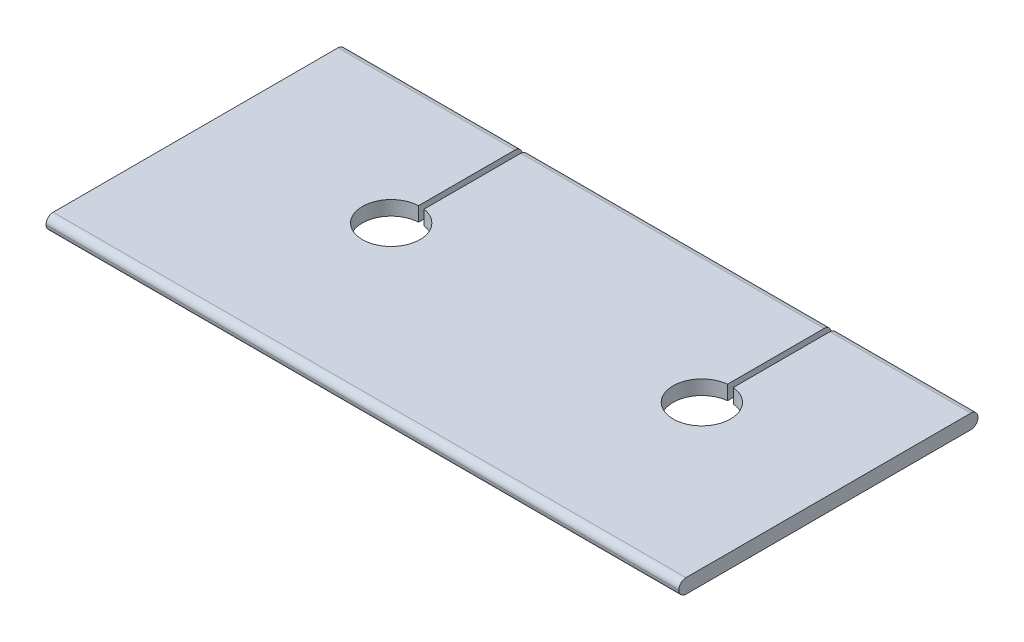
SolidWorks part; units mm, degrees
ref_plane "Front Plane" through (0, 0, 0) normal (0, 0, 1) x (1, 0, 0)
ref_plane "Top Plane" through (0, 0, 0) normal (0, 1, 0) x (1, 0, 0)
ref_plane "Right Plane" through (0, 0, 0) normal (1, 0, 0) x (0, 0, -1)
sketch "Sketch1" plane through (0, 0, 0) normal (1, 0, 0) x (0, 0, -1)
  line L1 (12.38, 0.625) -> (-12.38, 0.625)
  line L2 (13, 0.005) -> (13, -0.005)
  line L3 (12.38, -0.625) -> (-12.38, -0.625)
  line L4 (-13, 0.005) -> (-13, -0.005)
  line L5 (13, 0.625) -> (-13, -0.625) construction
  line L6 (13, -0.625) -> (-13, 0.625) construction
  arc A0 (13, -0.005) -> (12.38, -0.625) centre (12.38, -0.005) cw
  arc A1 (12.38, 0.625) -> (13, 0.005) centre (12.38, 0.005) cw
  arc A2 (-12.38, -0.625) -> (-13, -0.005) centre (-12.38, -0.005) cw
  arc A3 (-12.38, 0.625) -> (-13, 0.005) centre (-12.38, 0.005) ccw
  point P0 (0, 0)
  dimension "D3" = 0.62
  dimension "D1" = 26
  dimension "D2" = 1.25
extrude "Boss-Extrude1" add sketch "Sketch1" along normal blind 55
sketch "Sketch2" plane through (0, 0.625, 0) normal (0, 1, 0) x (1, 0, 0)
  line L0 (55, 13) -> (0, 13) construction
  line L2 (55, 12.38) -> (55, -12.38) construction
  line L3 (15.75, -13.4248) -> (15.25, -13.4248)
  line L4 (15.8823, 3.9706) -> (15.8823, 17.1341)
  line L5 (15.8823, 17.1341) -> (15.3823, 17.1341)
  line L6 (15.3823, 3.9972) -> (15.3823, 17.1341)
  line L9 (35.75, -13.4248) -> (35.25, -13.4248)
  line L10 (42.7463, 3.9878) -> (42.7463, 16.4248)
  line L11 (42.7463, 16.4248) -> (42.2463, 16.4248)
  line L12 (42.2463, 3.9871) -> (42.2463, 16.4248)
  arc A1 (42.2463, 3.9871) -> (42.7463, 3.9878) centre (42.5, 1.5) ccw
  arc A2 (15.3823, 3.9972) -> (15.8823, 3.9706) centre (15.5, 1.5) ccw
  line M4 (55, 12.38) -> (0, 12.38)
  dimension "D1" = 5
  dimension "D2" = 12.5
  dimension "D3" = 11.5
  dimension "D5" = 27
  dimension "D6" = 0.5
  dimension "D7" = 0.5
extrude "Cut-Extrude1" cut sketch "Sketch2" against normal through all contours L6 A2 L4 M4 | L12 A1 L10 M4 | L6 L4 L5 M4 | L12 L10 L11 M4
